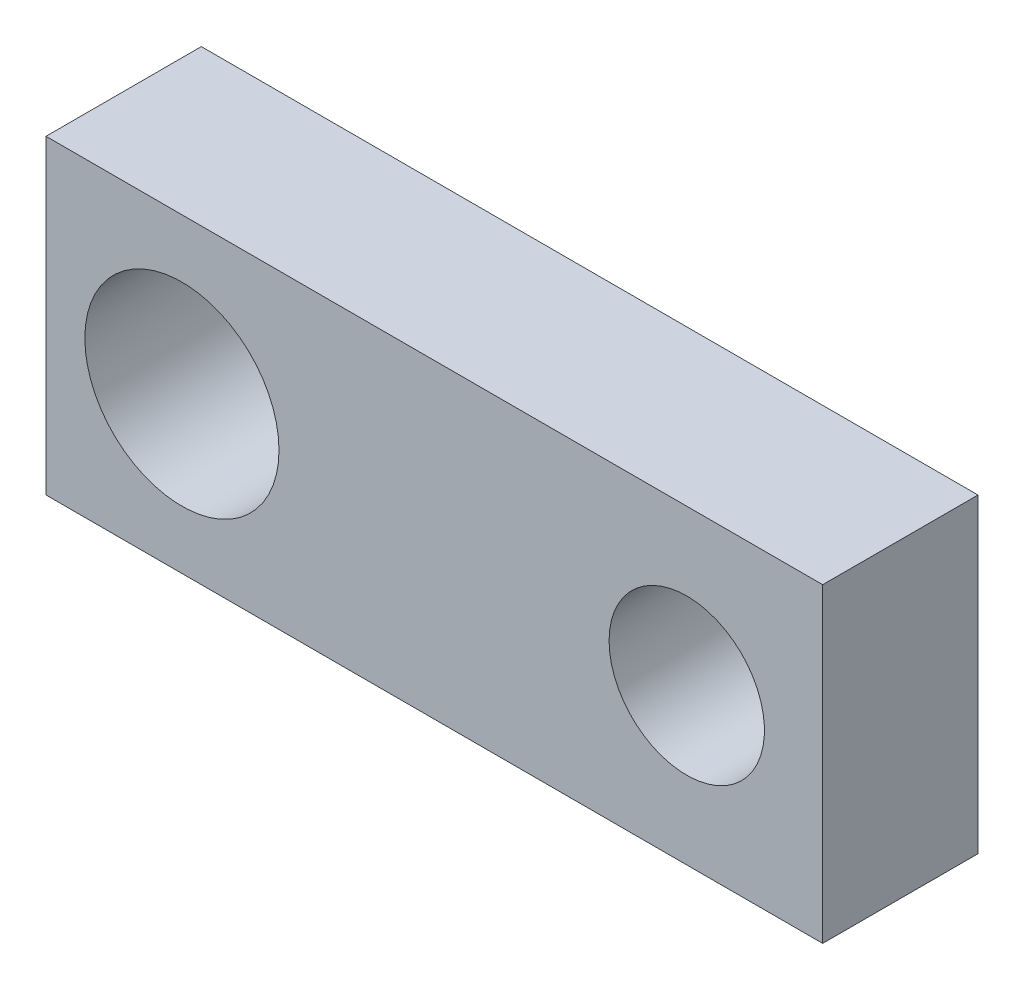
SolidWorks part; units mm, degrees
ref_plane "Plan de face" through (0, 0, 0) normal (0, 0, 1) x (1, 0, 0)
ref_plane "Plan de dessus" through (0, 0, 0) normal (0, 1, 0) x (1, 0, 0)
ref_plane "Plan de droite" through (0, 0, 0) normal (1, 0, 0) x (0, 0, -1)
sketch "Esquisse1" plane through (0, 0, 0) normal (0, 0, 1) x (1, 0, 0)
  line L0 (0, 0) -> (0, 8)
  line L1 (0, 8) -> (20, 8)
  line L2 (20, 8) -> (20, 0)
  line L3 (20, 0) -> (0, 0)
  circle A0 centre (3.5, 4) radius 2.5
  circle A1 centre (16.5, 4) radius 2
extrude "Extrusion1" add sketch "Esquisse1" along normal blind 4
